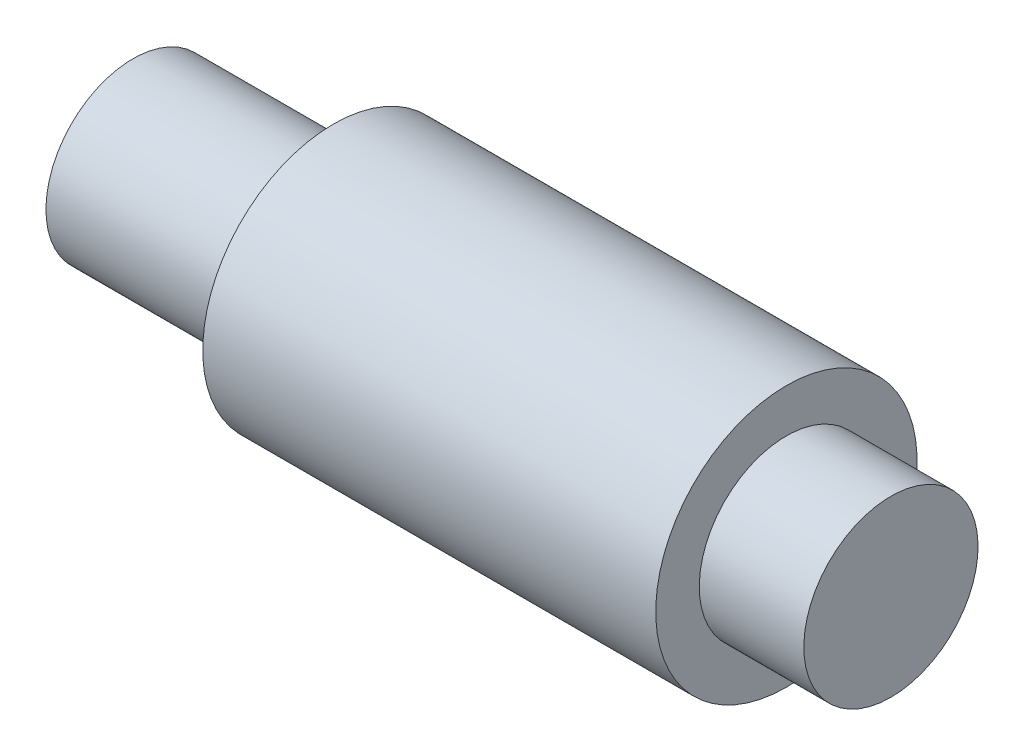
SolidWorks part; units mm, degrees
material "1060 Alloy"
ref_plane "Front Plane" through (0, 0, 0) normal (0, 0, 1) x (1, 0, 0)
ref_plane "Top Plane" through (0, 0, 0) normal (0, 1, 0) x (1, 0, 0)
ref_plane "Right Plane" through (0, 0, 0) normal (1, 0, 0) x (0, 0, -1)
sketch "Sketch1" plane through (0, 0, 0) normal (0, 0, 1) x (1, 0, 0)
  line L0 (0, 0) -> (0, -10)
  line L1 (0, -10) -> (87, -10)
  line L2 (87, -10) -> (87, 0)
  line L3 (87, 0) -> (75, 0)
  line L4 (75, 0) -> (75, 5)
  line L5 (75, 5) -> (23, 5)
  line L6 (23, 5) -> (23, 0)
  line L7 (23, 0) -> (0, 0)
  dimension "D1" = 10
  dimension "D2" = 5
  dimension "D3" = 12
  dimension "D4" = 23
  dimension "D5" = 52
revolve "Revolve1" add sketch "Sketch1" angle 360 about L1
